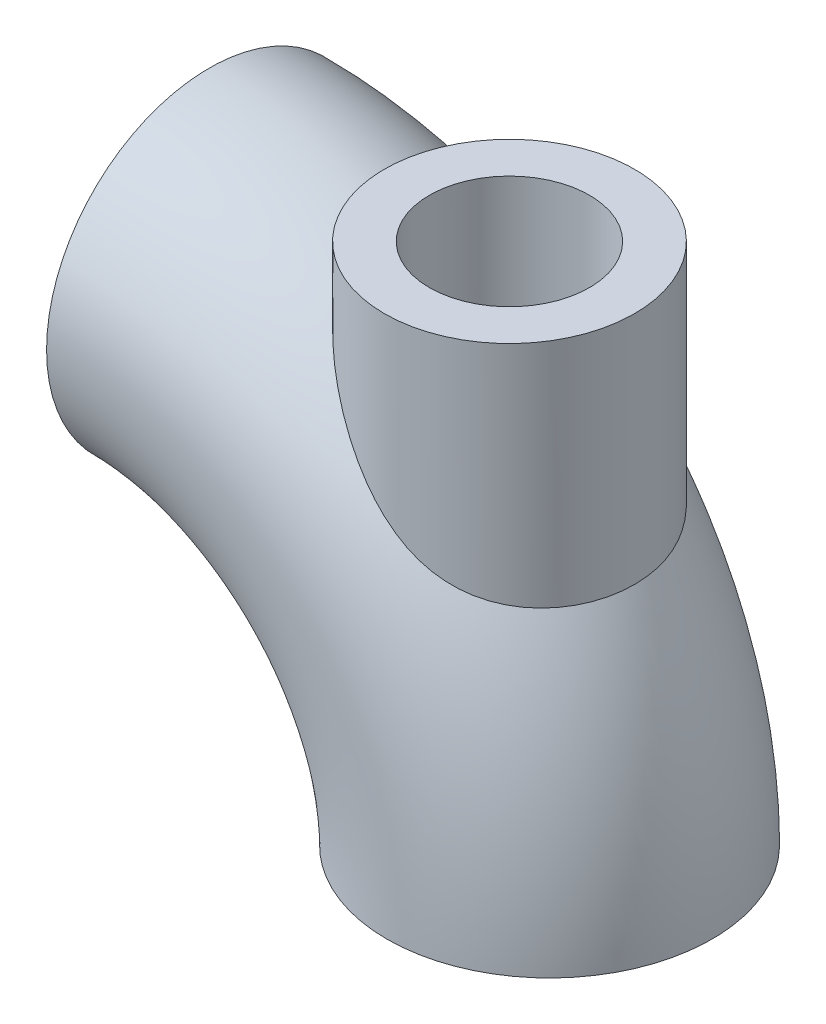
SolidWorks part; units mm, degrees
ref_plane "前视基准面" through (0, 0, 0) normal (0, 0, 1) x (1, 0, 0)
ref_plane "上视基准面" through (0, 0, 0) normal (0, 1, 0) x (1, 0, 0)
ref_plane "右视基准面" through (0, 0, 0) normal (1, 0, 0) x (0, 0, -1)
sketch "草图1" plane through (0, 0, 0) normal (0, 1, 0) x (1, 0, 0)
  circle A0 centre (0, 0) radius 32.5
  circle A1 centre (0, 0) radius 20
sketch "草图2" plane through (0, 0, 0) normal (0, 0, 1) x (1, 0, 0)
  line L2 (-136, 0) -> (-138.817, 0)
  arc A3 (0, 0) -> (-68, 68) centre (-68, 0) ccw
sweep "扫描1" add profiles "草图1" path "草图2"
sketch "草图3" plane through (0, 0, 0) normal (0, 0, 1) x (1, 0, 0)
  line L1 (-68, 100.5) -> (-8, 100.5)
ref_plane "基准面1" through (0, 100.5, 0) normal (0, 1, 0) x (1, 0, 0)
sketch "草图5" plane through (0, 100.5, 0) normal (0, 1, 0) x (1, 0, 0)
  line L0 (-68, 0) -> (-8, 0) construction
  circle A0 centre (-8, 0) radius 25
  circle A1 centre (-8, 0) radius 16
extrude "凸台-拉伸3" add sketch "草图5" against normal up to next contours A0
sketch "草图9" plane through (0, 100.5, 0) normal (0, 1, 0) x (1, 0, 0)
  circle A0 centre (-8, 0) radius 16
extrude "切除-拉伸3" cut sketch "草图9" against normal blind 80 contours A0
